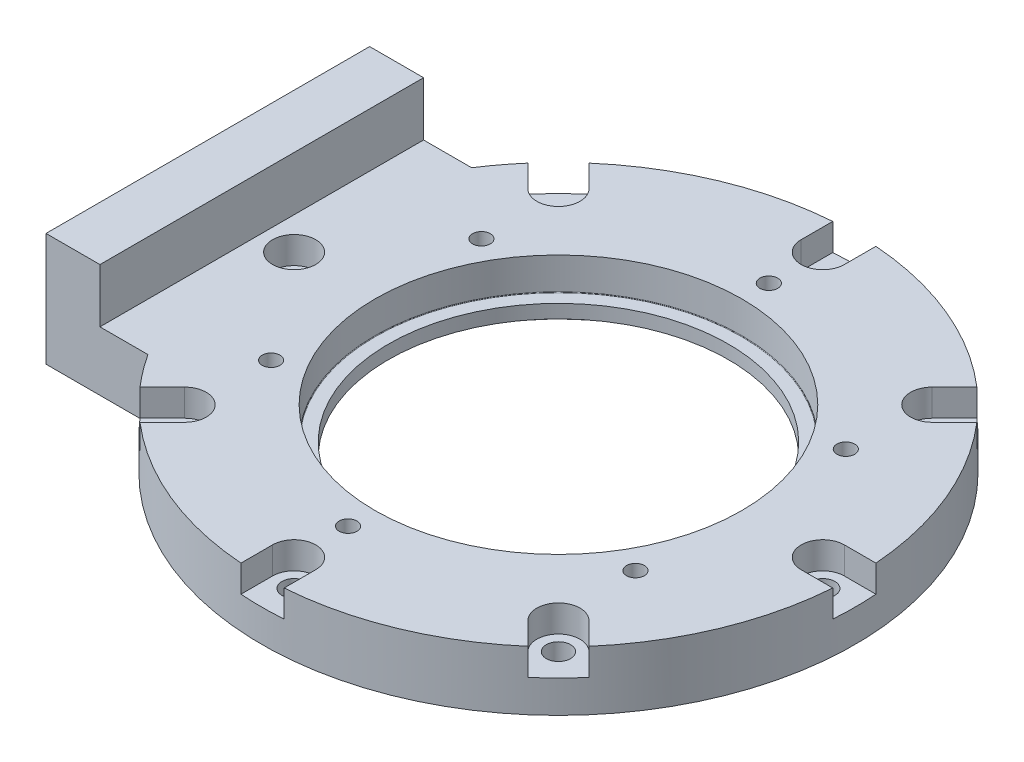
SolidWorks part; units mm, degrees
material "7075-T6, 플레이트 (SS)"
ref_plane "정면" through (0, 0, 0) normal (0, 0, 1) x (1, 0, 0)
ref_plane "윗면" through (0, 0, 0) normal (0, 1, 0) x (1, 0, 0)
ref_plane "우측면" through (0, 0, 0) normal (1, 0, 0) x (0, 0, -1)
sketch "스케치1" plane through (0, 0, 0) normal (0, 1, 0) x (1, 0, 0)
  line L1 (0, -55) -> (-65, -55)
  line L3 (0, 55) -> (-65, 55)
  line L4 (-65, -55) -> (-65, 55)
  line L5 (65, -55) -> (-65, 55) construction
  line L6 (65, 55) -> (-65, -55) construction
  arc A0 (0, -55) -> (0, 55) centre (0, 0) ccw
  circle A2 centre (0, 0) radius 35
  dimension "D1" = 110
  dimension "D4" = 70
  dimension "D2" = 110
  dimension "D3" = 130
extrude "보스-돌출1" add sketch "스케치1" along normal blind 2.5
sketch "스케치2" plane through (0, 2.5, 0) normal (0, 1, 0) x (1, 0, 0)
  line L0 (-65, 55) -> (-65, -55) construction
  line L1 (-65, -55) -> (0, -55) construction
  line L2 (0, 55) -> (-65, 55) construction
  line L3 (-65, 55) -> (-65, -55)
  line L4 (-65, -55) -> (0, -55)
  line L5 (0, 55) -> (-65, 55)
  circle A0 centre (0, 0) radius 31.5
  arc A1 (0, -55) -> (0, 55) centre (0, 0) ccw construction
  arc A2 (0, -55) -> (0, 55) centre (0, 0) ccw
  dimension "D1" = 63
extrude "보스-돌출2" add sketch "스케치2" along normal blind 2.5
sketch "스케치3" plane through (0, 5, 0) normal (0, 1, 0) x (1, 0, 0)
  line L0 (-65, 55) -> (-65, -55) construction
  line L1 (-65, -55) -> (0, -55) construction
  line L2 (0, 55) -> (-65, 55) construction
  line L3 (-65, 55) -> (-65, -55)
  line L4 (-65, -55) -> (0, -55)
  line L5 (0, 55) -> (-65, 55)
  circle A0 centre (0, 0) radius 34
  arc A1 (0, -55) -> (0, 55) centre (0, 0) ccw construction
  arc A2 (0, -55) -> (0, 55) centre (0, 0) ccw
  dimension "D1" = 68
extrude "보스-돌출3" add sketch "스케치3" along normal blind 6
sketch "스케치5" plane through (0, 11, 0) normal (0, 1, 0) x (1, 0, 0)
  circle A0 centre (0, 0) radius 49 construction
  circle A1 centre (0, 0) radius 39 construction
  point P4 (0, 39)
  point P5 (0, 49)
  dimension "D1" = 98
  dimension "D2" = 78
hole_wizard "M4 육각 소켓 머리 캡 나사용 카운터보어1" positions "스케치6" profile "스케치8" counterbore size "M4" standard "ISO" end condition through all
sketch "스케치6" plane through (0, 11, 0) normal (0, 1, 0) x (1, 0, 0)
  point P0 (0, 49)
sketch "스케치8" plane through (0, 11, -49) normal (1, 0, 0) x (0, 0, 1)
  line L0 (0, 0) -> (0, 11)
  line L1 (0, 11) -> (2.25, 11)
  line L3 (2.25, 11) -> (2.25, 5)
  line L4 (2.25, 5) -> (4, 5)
  line L5 (4, 5) -> (4, 0)
  line L7 (4, 0) -> (0, 0)
  line L11 (0, -6.35) -> (0, 107.95) construction
  dimension "관통 구멍 지름" = 4.5
  dimension "관통 구멍 깊이" = 11
  dimension "카운터보어 지름" = 8
  dimension "카운터보어 깊이" = 5
hole_wizard "M4 탭을 위한 탭 드릴1" positions "스케치9" profile "스케치10" hole size "M4" standard "ISO" end condition through all
sketch "스케치9" plane through (0, 11, 0) normal (0, 1, 0) x (1, 0, 0)
  point P0 (0, 39)
sketch "스케치10" plane through (0, 11, -39) normal (1, 0, 0) x (0, 0, 1)
  line L0 (0, 0) -> (0, 11)
  line L1 (0, 11) -> (1.65, 11)
  line L2 (1.65, 11) -> (1.65, 0)
  line L5 (1.65, 0) -> (0, 0)
  line L11 (0, -6.35) -> (0, 107.95) construction
  dimension "관통 구멍 지름" = 3.3
  dimension "관통 구멍 깊이" = 11
pattern_circular "원형 패턴1" count 8 over 360 about axis through (0, 0, 0) along (0, 1, 0) of "M4 육각 소켓 머리 캡 나사용 카운터보어1"
pattern_circular "원형 패턴2" count 6 over 360 about axis through (0, 0, 0) along (0, 1, 0) of "M4 탭을 위한 탭 드릴1"
sketch "스케치11" plane through (0, 11, 0) normal (0, 1, 0) x (1, 0, 0)
  line L1 (4, 61) -> (-4, 61)
  line L2 (4, 61) -> (4, 49)
  line L3 (4, 49) -> (-4, 49)
  line L4 (-4, 61) -> (-4, 49)
  line L5 (4, 61) -> (-4, 49) construction
  line L6 (4, 49) -> (-4, 61) construction
  circle A2 centre (0, 49) radius 4 construction
  circle A3 centre (0, 49) radius 4 construction
  point P0 (0, 55)
extrude "컷-돌출1" cut sketch "스케치11" against normal mid plane 10
sketch "스케치12" plane through (0, 11, 0) normal (0, 1, 0) x (1, 0, 0)
  line L5 (-65, 55) -> (-65, -55) construction
  line L6 (-65, -30) -> (-55, -30)
  line L7 (-65, -30) -> (-65, 30)
  line L8 (-65, 30) -> (-55, 30)
  line L9 (-55, -30) -> (-55, 30)
  line L10 (-65, -55) -> (0, -55) construction
  line L11 (-4, 55) -> (-65, 55) construction
  dimension "D1" = 10
  dimension "D2" = 25
  dimension "D3" = 25
extrude "보스-돌출4" add sketch "스케치12" along normal blind 10
sketch "스케치13" plane through (0, 11, 0) normal (0, 1, 0) x (1, 0, 0)
  line L1 (-65, -30) -> (-46.0977, -30)
  line L2 (-65, -30) -> (-65, 30)
  line L3 (-65, 30) -> (-46.0977, 30)
  line L5 (100, -65) -> (-100, -65)
  line L6 (100, -65) -> (100, 65)
  line L7 (100, 65) -> (-100, 65)
  line L8 (-100, -65) -> (-100, 65)
  line L9 (100, -65) -> (-100, 65) construction
  line L10 (100, 65) -> (-100, -65) construction
  arc A0 (-46.0977, -30) -> (-46.0977, 30) centre (0, 0) ccw
  dimension "D1" = 110
  dimension "D2" = 65
  dimension "D3" = 200
  dimension "D4" = 30
  dimension "D5" = 30
  dimension "D6" = 130
extrude "컷-돌출2" cut sketch "스케치13" against normal through all
pattern_circular "원형 패턴3" count 8 over 360 about axis through (0, 0, 0) along (0, 1, 0) skipping 2 of "컷-돌출1"
fillet "필렛1" radius 0.1 2 edges at (0, 5, 34) (0, 2.5, 35)
